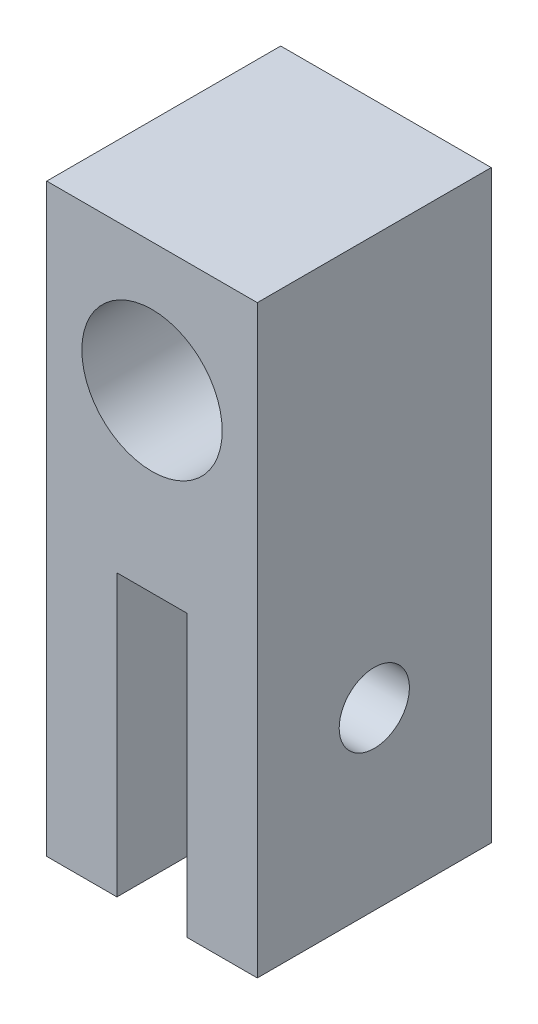
SolidWorks part; units mm, degrees
ref_plane "Front Plane" through (0, 0, 0) normal (0, 0, 1) x (1, 0, 0)
ref_plane "Top Plane" through (0, 0, 0) normal (0, 1, 0) x (1, 0, 0)
ref_plane "Right Plane" through (0, 0, 0) normal (1, 0, 0) x (0, 0, -1)
sketch "Sketch1" plane through (0, 0, 0) normal (0, 0, 1) x (1, 0, 0)
  line L0 (0, -0.5) -> (0, 7)
  line L1 (-4.5, -12.5) -> (4.5, -12.5)
  line L2 (-4.5, -12.5) -> (-4.5, 12.5)
  line L3 (-4.5, 12.5) -> (4.5, 12.5)
  line L4 (4.5, -12.5) -> (4.5, 12.5)
  line L5 (-4.5, -12.5) -> (4.5, 12.5) construction
  line L6 (-4.5, 12.5) -> (4.5, -12.5) construction
  line L8 (-1.5, -12.5) -> (1.5, -12.5)
  line L9 (-1.5, -12.5) -> (-1.5, -0.5)
  line L10 (-1.5, -0.5) -> (1.5, -0.5)
  line L11 (1.5, -12.5) -> (1.5, -0.5)
  circle A0 centre (0, 7) radius 3
  point P0 (0, 0)
  point P9 (0, -12.5)
  dimension "D1" = 9
  dimension "D2" = 25
extrude "Boss-Extrude1" add sketch "Sketch1" along normal blind 10
ref_plane "Plane1" through (4.5, 0, 0) normal (1, 0, 0) x (0, 0, -1)
sketch "Sketch3" plane through (4.5, 0, 0) normal (1, 0, 0) x (0, 0, -1)
  line L0 (-5, -12.5) -> (-5, -5) construction
  line L1 (-10, -12.5) -> (0, -12.5) construction
  circle A0 centre (-5, -5) radius 1.5
extrude "Cut-Extrude1" cut sketch "Sketch3" against normal through all both and the other way through all
